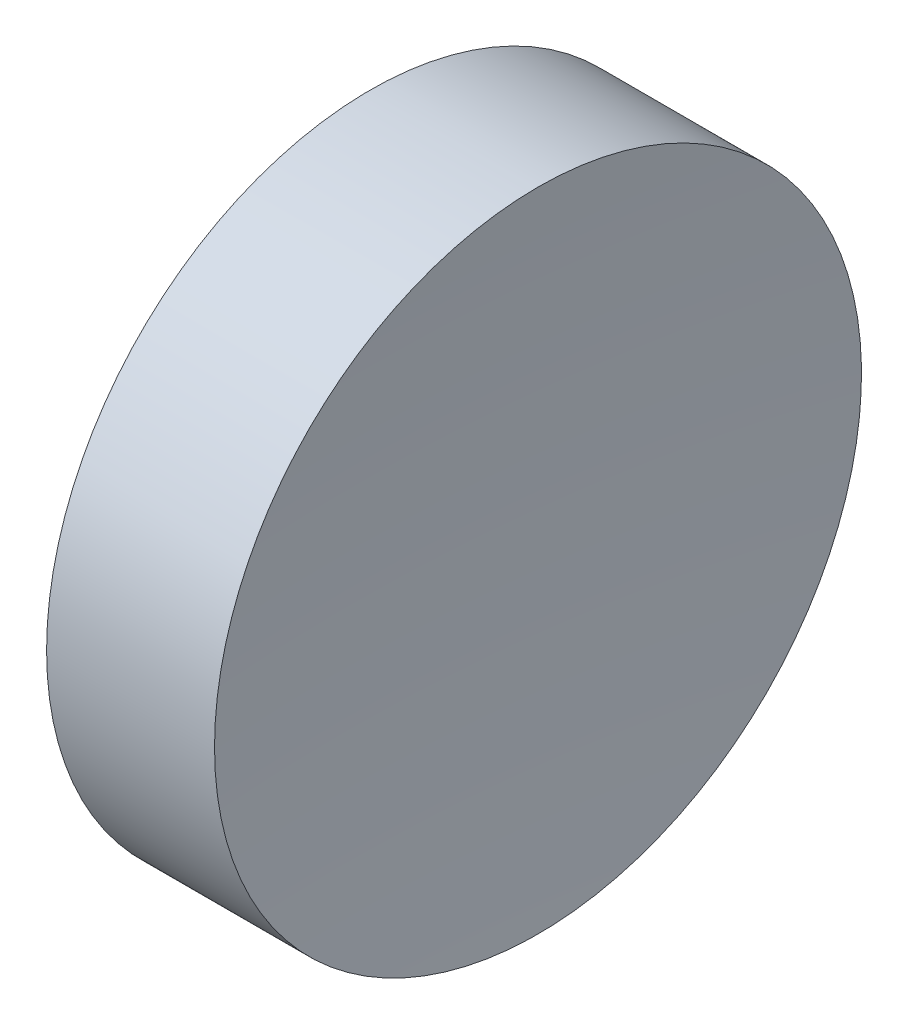
SolidWorks part; units mm, degrees
ref_plane "前视基准面" through (0, 0, 0) normal (0, 0, 1) x (1, 0, 0)
ref_plane "上视基准面" through (0, 0, 0) normal (0, 1, 0) x (1, 0, 0)
ref_plane "右视基准面" through (0, 0, 0) normal (1, 0, 0) x (0, 0, -1)
sketch "草图1" plane through (0, 0, 0) normal (0, 0, 1) x (1, 0, 0)
  line L0 (54.4926, 34.689) -> (66.3882, 34.689) construction
  line L1 (57.5463, 34.689) -> (57.5463, 40.939)
  line L2 (57.5463, 40.939) -> (60.7908, 40.939)
  line L3 (60.5463, 34.689) -> (57.5463, 34.689)
  arc A0 (60.7908, 40.939) -> (60.5463, 34.689) centre (140.5463, 34.689) ccw
revolve "旋转1" add sketch "草图1" angle 360 about L0
